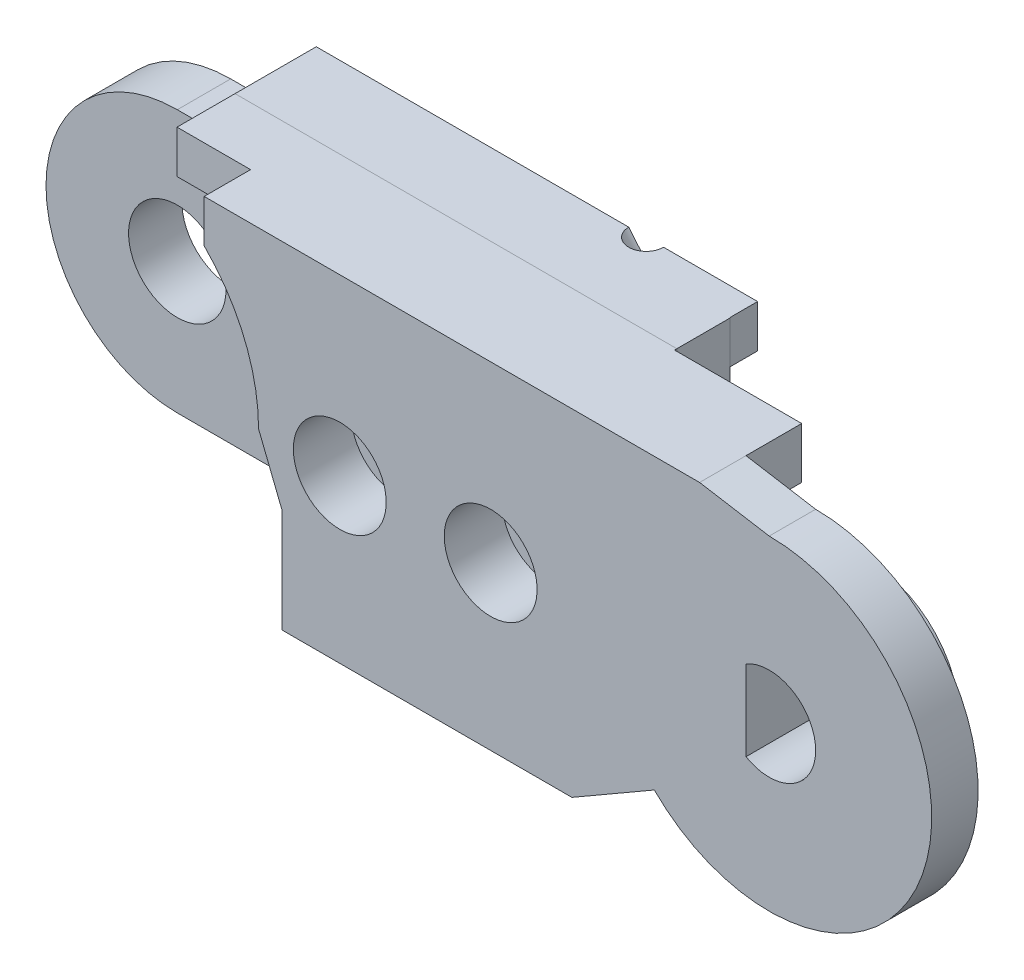
SolidWorks part; units mm, degrees
ref_plane "Front Plane" through (0, 0, 0) normal (0, 0, 1) x (1, 0, 0)
ref_plane "Top Plane" through (0, 0, 0) normal (0, 1, 0) x (1, 0, 0)
ref_plane "Right Plane" through (0, 0, 0) normal (1, 0, 0) x (0, 0, -1)
sketch "Sketch3" plane through (0, 0, 0) normal (0, 0, 1) x (1, 0, 0)
  line L7 (8, 0) -> (9, -2.5)
  line L11 (30, 7) -> (27, 7.5)
  line L13 (0, 7) -> (0, 7.5) construction
  line L14 (0, 7.5) -> (-22.3287, 7.5) construction
  line L15 (0, 5.3) -> (-14, 5.3) construction
  line L16 (0, 4) -> (-14, 4) construction
  line L17 (-14, 4) -> (-14, 5.3) construction
  line L18 (5.6569, 5.6569) -> (5.6569, 7.5)
  line L19 (5.6569, 7.5) -> (27, 7.5)
  line L20 (21.5, -7) -> (9, -7)
  line L21 (9, -7) -> (9, -2.5)
  line L23 (25.0503, -4.9497) -> (21.5, -7)
  arc A4 (8, 0) -> (5.6569, 5.6569) centre (0, 0) ccw
  arc A5 (25.0503, -4.9497) -> (30, 7) centre (30, 0) ccw
  circle A6 centre (0, 0) radius 7 construction
  circle A7 centre (0, 0) radius 3.9 construction
  circle A8 centre (0, 0) radius 5.3 construction
  circle A9 centre (0, 0) radius 4 construction
  dimension "D10" = 0.5
  dimension "D17" = 14
  dimension "D5" = 135
  dimension "D6" = 12.5
  dimension "D7" = 4.5
  dimension "D8" = 1
  dimension "D9" = 45
  dimension "D11" = 1.8431
  dimension "D12" = 30
  dimension "D14" = 3
extrude "Boss-Extrude1" add sketch "Sketch3" along normal blind 2 contours A5 L11 L19 L18 A4 L7 L21 L20 L23
sketch "Sketch20" plane through (0, 0, 0) normal (0, 0, 1) x (1, 0, 0)
  line L0 (0, 7) -> (0, 7.5) construction
  line L1 (0, 7.5) -> (-19.4737, 7.5) construction
  line L2 (0, 5.3) -> (-14, 5.3) construction
  line L3 (0, 4) -> (-14, 4) construction
  line L4 (-14, 4) -> (-14, 5.3) construction
  line L5 (0, 5.3) -> (17.4849, 5.3) construction
  line L6 (17.4849, 5.3) -> (17.4849, 4) construction
  line L7 (17.4849, 4) -> (0, 4) construction
  line L8 (-2.5, 7.5) -> (-2.5, 2.868) construction
  circle A0 centre (0, 0) radius 7 construction
  circle A1 centre (0, 0) radius 3.9 construction
  circle A3 centre (0, 0) radius 5.3 construction
  circle A4 centre (0, 0) radius 4 construction
  circle A5 centre (0, 0) radius 2 construction
  dimension "D1" = 0
  dimension "D2" = 2.5
ref_plane "Plane1" through (0, 0, 2) normal (0, 0, 1) x (1, 0, 0)
sketch "Sketch4" plane through (0, 0, 2) normal (0, 0, 1) x (1, 0, 0)
  line L4 (5.6569, 5.6569) -> (5.6569, 7.5)
  line L5 (5.6569, 5.6569) -> (5.6569, 7.5) construction
  line L6 (5.6569, 7.5) -> (21.5, 7.5)
  line L10 (8, 0) -> (9, -2.5)
  line L11 (9, -2.5) -> (9, -7)
  line L12 (9, -7) -> (21.5, -7)
  line L13 (21.5, -7) -> (21.5, 7.5)
  arc A0 (8, 0) -> (5.6569, 5.6569) centre (0, 0) ccw construction
  arc A3 (8, 0) -> (5.6569, 5.6569) centre (0, 0) ccw
sketch "Sketch22" plane through (0, 0, 2) normal (0, 0, 1) x (1, 0, 0)
  line L0 (5.6569, 5.6569) -> (2.4868, 5.6569)
  line L1 (5.6569, 7.5) -> (21.5, 7.5)
  line L2 (5.6569, 7.5) -> (2.4868, 7.5)
  line L3 (2.4868, 7.5) -> (2.4868, 5.6569)
  line L6 (8, 0) -> (9, -2.5)
  line L7 (9, -2.5) -> (9, -7)
  line L8 (9, -7) -> (21.5, -7)
  line L10 (21.5, 7.5) -> (27, 7.5)
  line L11 (27, 7.5) -> (27, 2.172)
  line L12 (27, 2.172) -> (23.2751, 2.172)
  line L13 (21.5, -7) -> (23.2751, -5.9749)
  line L14 (25.0503, -4.9497) -> (21.5, -7) construction
  line L15 (23.2751, -5.9749) -> (23.2751, 2.172)
  arc A0 (8, 0) -> (5.6569, 5.6569) centre (0, 0) ccw
extrude "Boss-Extrude6" add sketch "Sketch22" along normal blind 2.5
sketch "Sketch25" plane through (0, 0, 2) normal (0, 0, 1) x (1, 0, 0)
  line L0 (0, 5.3) -> (18.0981, 5.3) construction
  line L1 (0, 4) -> (18.0981, 4) construction
  line L2 (18.0981, 4) -> (18.0981, 5.3) construction
sketch "Sketch26" plane through (0, 0, 2) normal (0, 0, 1) x (1, 0, 0)
  line L1 (18.0981, 5.3) -> (2.5301, 5.3)
  line L2 (18.0981, 4) -> (2.5301, 4)
  line L3 (2.5301, 5.3) -> (2.5301, 4)
  line L4 (18.0981, 5.3) -> (27, 5.3)
  line L5 (27, 2.172) -> (27, 7.5) construction
  line L6 (27, 5.3) -> (27, 4)
  line L7 (27, 4) -> (18.0981, 4)
extrude "Cut-Extrude6" cut sketch "Sketch26" along normal blind 2.5
ref_plane "Plane18" through (0, 0, 4.5) normal (0, 0, 1) x (1, 0, 0)
sketch "Sketch31" plane through (0, 0, 4.5) normal (0, 0, 1) x (1, 0, 0)
  line L0 (2.4327, 5.6569) -> (0, 5.6569)
  line L4 (9, -5.6569) -> (0, -5.6569)
  line L5 (2.4327, 5.6569) -> (2.4868, 7.5)
  line L12 (9, -7) -> (9, -5.6569)
  line L13 (9, -2.5) -> (9, -7) construction
  line L16 (27, 7.5) -> (27, 2.172)
  line L17 (27, 2.172) -> (23.2751, 2.172)
  line L18 (23.2751, -5.9749) -> (23.2751, 2.172)
  line L19 (27, 7.5) -> (2.4868, 7.5)
  line L20 (9, -7) -> (21.5, -7)
  line L21 (21.5, -7) -> (23.2751, -5.9749)
  arc A0 (0, 5.6569) -> (0, -5.6569) centre (0, 0) ccw
  dimension "D1" = 5.6569
extrude "Boss-Extrude14" add sketch "Sketch31" along normal blind 2.3 separate body
sketch "Sketch32" plane through (0, 0, 6.8) normal (0, 0, 1) x (1, 0, 0)
  circle A0 centre (0, 0) radius 2.1
extrude "Cut-Extrude7" cut sketch "Sketch32" against normal blind 2.3
sketch "Sketch33" plane through (0, 0, 6.8) normal (0, 0, 1) x (1, 0, 0)
  line L4 (9, -5.6569) -> (9, -7)
  line L11 (9, -7) -> (21.5, -7)
  line L15 (21.5, -7) -> (21.5, -5.6569)
  line L16 (21.5, -5.6569) -> (9, -5.6569)
  line L17 (2.4868, 7.5) -> (21.5, 7.5)
  line L18 (27, 7.5) -> (2.4868, 7.5) construction
  line L19 (2.4868, 7.5) -> (2.4327, 5.6569)
  line L20 (2.4327, 5.6569) -> (21.5, 5.6569)
  line L21 (21.5, 5.6569) -> (21.5, 7.5)
extrude "Boss-Extrude15" add sketch "Sketch33" along normal blind 1.2
sketch "Sketch34" plane through (0, 0, 2) normal (0, 0, 1) x (1, 0, 0)
  line L0 (30, 5.3) -> (18.0981, 5.3) construction
  line L1 (30, 4) -> (18.0981, 4) construction
  circle A0 centre (30, 0) radius 2 construction
  circle A1 centre (30, 0) radius 5.3 construction
  circle A2 centre (30, 0) radius 4 construction
sketch "Sketch35" plane through (0, 0, 6.8) normal (0, 0, 1) x (1, 0, 0)
  line L0 (27, 2.172) -> (27, 7.5)
  line L1 (27, 2.172) -> (21.5204, 2.172)
  line L2 (27, 7.5) -> (21.5204, 7.5)
  line L3 (21.5204, 2.172) -> (21.5204, 7.5)
  line L4 (27, 2.172) -> (27, 7.5) construction
  line L5 (27, 7.5) -> (21.5, 7.5) construction
  dimension "D1" = 0
extrude "Cut-Extrude8" cut sketch "Sketch35" against normal blind 2.4
sketch "Sketch36" plane through (0, 0, 4.4) normal (0, 0, 1) x (1, 0, 0)
  line L0 (27, 2.172) -> (27, 4)
  line L1 (27, 2.172) -> (23.3, 2.172)
  line L2 (27, 4) -> (23.3, 4)
  line L3 (23.3, 2.172) -> (23.3, 4)
  line L4 (21.5, -7) -> (21.5, 7.5) construction
  dimension "D1" = 1.8
extrude "Cut-Extrude9" cut sketch "Sketch36" against normal blind 2.4
sketch "Sketch37" plane through (0, 0, 2) normal (0, 0, 1) x (1, 0, 0)
  circle A0 centre (30, 0) radius 3.9
extrude "Boss-Extrude16" add sketch "Sketch37" along normal blind 2.3
sketch "Sketch39" plane through (0, 0, 4.3) normal (0, 0, 1) x (1, 0, 0)
  line L0 (29, 1.7321) -> (29, -1.7321)
  arc A0 (29, -1.7321) -> (29, 1.7321) centre (30, 0) ccw
  dimension "D2" = 4
  dimension "D1" = 1
extrude "Cut-Extrude10" cut sketch "Sketch39" against normal through all
sketch "Sketch43" plane through (0, 0, 6.8) normal (0, 0, 1) x (1, 0, 0)
  line L2 (0, -5.6569) -> (9, -5.6569) construction
  circle A0 centre (11.5, 0) radius 2.5
  circle A1 centre (18, 0) radius 2.5
  dimension "D1" = 2.5
  dimension "D3" = 5
  dimension "D4" = 6.5
  dimension "D2" = 5.6569
extrude "Boss-Extrude17" add sketch "Sketch43" along normal blind 1.2
sketch "Sketch44" plane through (0, 0, 8) normal (0, 0, 1) x (1, 0, 0)
  circle A0 centre (11.5, 0) radius 0.95
  circle A1 centre (18, 0) radius 0.95
  dimension "D1" = 1.9
  dimension "D2" = 1.9
extrude "Cut-Extrude11" cut sketch "Sketch44" against normal through all
sketch "Sketch45" plane through (0, 0, 0) normal (0, 0, -1) x (-1, 0, 0)
  circle A0 centre (-11.5, 0) radius 2
  circle A1 centre (-18, 0) radius 2
extrude "Cut-Extrude12" cut sketch "Sketch45" against normal blind 2.5
ref_plane "Plane17" through (0, 0, 8) normal (0, 0, 1) x (1, 0, 0)
sketch "Sketch48" plane through (0, 0, 2) normal (0, 0, 1) x (1, 0, 0)
  circle A0 centre (30, 0) radius 5 construction
sketch "Sketch51" plane through (0, 0, 8) normal (0, 0, 1) x (1, 0, 0)
  line L0 (18.2355, 5.6569) -> (27.0112, -4.8677) construction
  line L1 (2.4327, 5.6569) -> (21.5, 5.6569) construction
sketch "Sketch52" plane through (0, 5.6569, 0) normal (0, -1, 0) x (1, 0, 0)
  circle A0 centre (18.2355, 8) radius 0.75
extrude "Cut-Extrude13" cut sketch "Sketch52" along direction (0.6404, -0.768, 0) on the side against the normal blind 10
split "Split1" trim tools "Plane18" bodies to split 133 129 resulting bodies 135 136
mirror "Mirror1" about plane through (0, 0, 8) normal (0, 0, 1) of bodies 135 136
delete or keep bodies "Body-Delete/Keep 1" type delete bodies bodies 135 136
